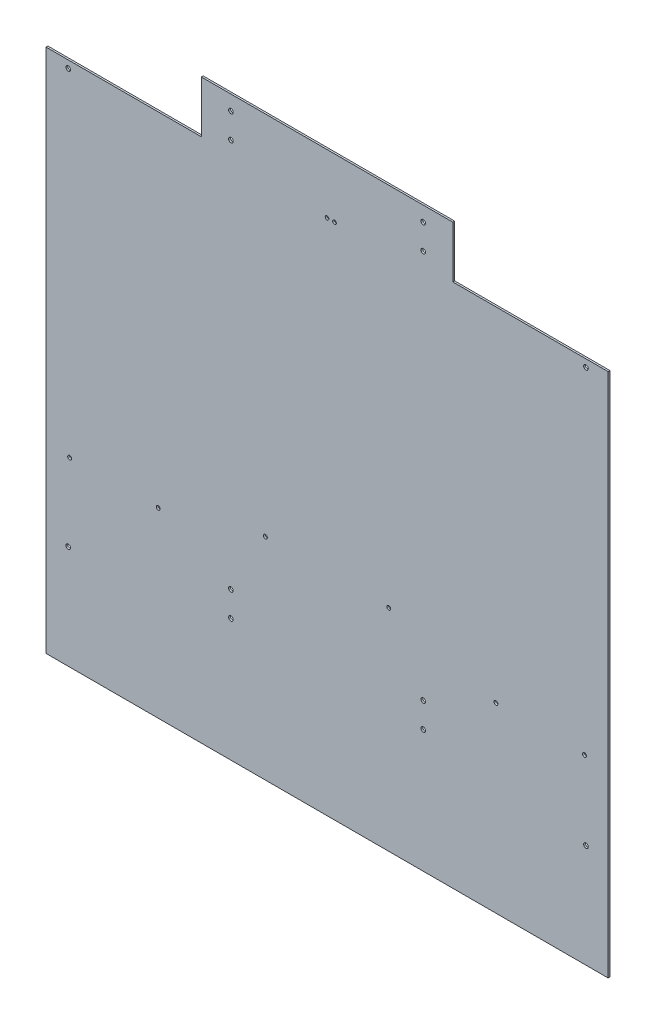
SolidWorks part; units mm, degrees
material "PC High Viscosity"
ref_plane "Front Plane" through (0, 0, 0) normal (0, 0, 1) x (1, 0, 0)
ref_plane "Top Plane" through (0, 0, 0) normal (0, 1, 0) x (1, 0, 0)
ref_plane "Right Plane" through (0, 0, 0) normal (1, 0, 0) x (0, 0, -1)
sketch "Sketch2" plane through (0, 0, 0) normal (0, 0, 1) x (1, 0, 0)
  line L0 (-482.6, 901.7) -> (-215.9, 901.7)
  line L1 (-482.6, 0) -> (482.6, 0)
  line L2 (-482.6, 0) -> (-482.6, 901.7)
  line L4 (482.6, 0) -> (482.6, 901.7)
  line L5 (-215.9, 901.7) -> (-215.9, 990.6)
  line L6 (-215.9, 990.6) -> (215.9, 990.6)
  line L7 (215.9, 990.6) -> (215.9, 901.7)
  line L8 (215.9, 901.7) -> (482.6, 901.7)
  line L9 (0, 0) -> (0, 990.6) construction
  dimension "D1" = 990.6
  dimension "D2" = 965.2
  dimension "D3" = 88.9
  dimension "D4" = 431.8
extrude "Boss-Extrude1" add sketch "Sketch2" along normal blind 3.175
hole_wizard "1/4 Clearance Hole1" positions "Sketch3" profile "Sketch4" hole size "1/4" standard "ANSI Inch" end condition through all
sketch "Sketch3" plane through (0, 0, 3.175) normal (0, 0, 1) x (1, 0, 0)
  line L0 (0, 0) -> (0, 990.6) construction
  line L1 (-482.6, 0) -> (482.6, 0) construction
  line L4 (-9.861, 373.4082) -> (0, 410.21) construction
  line L5 (-9.861, 373.4082) -> (472.739, 244.0959) construction
  line L6 (0, 410.21) -> (482.6, 280.8977) construction
  line L7 (472.739, 244.0959) -> (482.6, 280.8977) construction
  line L8 (482.6, 0) -> (482.6, 901.7) construction
  line L9 (12.7, 406.807) -> (2.839, 370.0053) construction
  line L11 (-4.9305, 391.8091) -> (477.6695, 262.4968) construction
  line L14 (0, 410.21) -> (1.6435, 416.3436) construction
  line L15 (0, 410.21) -> (480.9565, 281.3381) construction
  line L16 (1.6435, 416.3436) -> (482.6, 287.4717) construction
  line L17 (480.9565, 281.3381) -> (482.6, 287.4717) construction
  line L18 (215.9, 990.6) -> (-215.9, 990.6) construction
  circle A0 centre (441.96, 311.5092) radius 6.35 construction
  point P178 (105.9076, 362.1101)
  point P180 (289.9164, 312.8051)
  point P183 (-289.9164, 312.8051)
  point P184 (-105.9076, 362.1101)
  point P566 (441.96, 311.5092)
  point P569 (-441.96, 311.5092)
  dimension "D10" = 12.7
  dimension "D11" = 6.35
  dimension "D1" = 15
  dimension "D2" = 12.7
  dimension "D3" = 38.1
  dimension "D4" = 410.21
  dimension "D5" = 101.6
  dimension "D6" = 292.1
  dimension "D9" = 6.35
  dimension "D12" = 439.2982
  dimension "D7" = 441.96
sketch "Sketch4" plane through (-441.96, 311.5092, 3.175) normal (1, 0, 0) x (0, -1, 0)
  line L0 (0, 0) -> (0, 3.175)
  line L1 (0, 3.175) -> (3.3782, 3.175)
  line L2 (3.3782, 3.175) -> (3.3782, 0)
  line L5 (3.3782, 0) -> (0, 0)
  line L11 (0, -6.35) -> (0, 107.95) construction
  dimension "Thru Hole Dia." = 6.7564
  dimension "Thru Hole Depth" = 3.175
hole_wizard "5/16 (0.3125) Diameter Hole1" positions "Sketch5" profile "Sketch6" hole size "5/16" standard "ANSI Inch" end condition through all
sketch "Sketch5" plane through (0, 0, 3.175) normal (0, 0, 1) x (1, 0, 0)
  line L1 (-215.9, 962.66) -> (215.9, 962.66) construction
  line L2 (-215.9, 962.66) -> (-215.9, 924.56) construction
  line L3 (-215.9, 924.56) -> (215.9, 924.56) construction
  line L4 (215.9, 962.66) -> (215.9, 924.56) construction
  line L5 (-215.9, 990.6) -> (-215.9, 901.7) construction
  line L6 (215.9, 901.7) -> (215.9, 990.6) construction
  line L7 (0, 990.6) -> (0, 0) construction
  line L8 (215.9, 990.6) -> (-215.9, 990.6) construction
  line L9 (-482.6, 0) -> (482.6, 0) construction
  line L10 (165.1, 922.02) -> (165.1, 210.82) construction
  point P0 (-165.1, 922.02)
  point P2 (-165.1, 965.2)
  point P4 (165.1, 965.2)
  point P6 (165.1, 922.02)
  point P125 (-165.1, 210.82)
  point P126 (-165.1, 254)
  point P127 (165.1, 254)
  point P128 (165.1, 210.82)
  point P131 (-444.5, 177.8)
  point P137 (444.5, 177.8)
  point P150 (-444.5, 889)
  point P151 (444.5, 889)
  dimension "D1" = 38.1
  dimension "D2" = 2.54
  dimension "D3" = 2.54
  dimension "D4" = 924.56
  dimension "D5" = 50.8
  dimension "D7" = 711.2
  dimension "D8" = 177.8
  dimension "D11" = 711.2
  dimension "D9" = 444.5
  dimension "D6" = 2
  dimension "D10" = 2
sketch "Sketch6" plane through (-165.1, 922.02, 3.175) normal (1, 0, 0) x (0, -1, 0)
  line L0 (0, 0) -> (0, 3.175)
  line L1 (0, 3.175) -> (3.9688, 3.175)
  line L2 (3.9688, 3.175) -> (3.9688, 0)
  line L5 (3.9688, 0) -> (0, 0)
  line L11 (0, -6.35) -> (0, 107.95) construction
  dimension "Thru Hole Dia." = 7.9375
  dimension "Thru Hole Depth" = 3.175
hole_wizard "1/4 (0.25) Diameter Hole1" positions "Sketch7" profile "Sketch8" hole size "1/4" standard "ANSI Inch" end condition through all
sketch "Sketch7" plane through (0, 0, 3.175) normal (0, 0, 1) x (1, 0, 0)
  line L0 (-482.6, 0) -> (482.6, 0) construction
  line L1 (215.9, 990.6) -> (-215.9, 990.6) construction
  point P0 (0, 889)
  point P6 (0, 0)
  point P9 (12.7, 889)
  point P12 (8.9692, 897.9913)
  point P13 (0, 0)
  dimension "D1" = 101.6
  dimension "D2" = 12.7
sketch "Sketch8" plane through (0, 889, 3.175) normal (1, 0, 0) x (0, -1, 0)
  line L0 (0, 0) -> (0, 3.175)
  line L1 (0, 3.175) -> (3.175, 3.175)
  line L2 (3.175, 3.175) -> (3.175, 0)
  line L5 (3.175, 0) -> (0, 0)
  line L11 (0, -6.35) -> (0, 107.95) construction
  dimension "Thru Hole Dia." = 6.35
  dimension "Thru Hole Depth" = 3.175
equation "\"D3@Sketch5\"=\"D2@Sketch5\""
